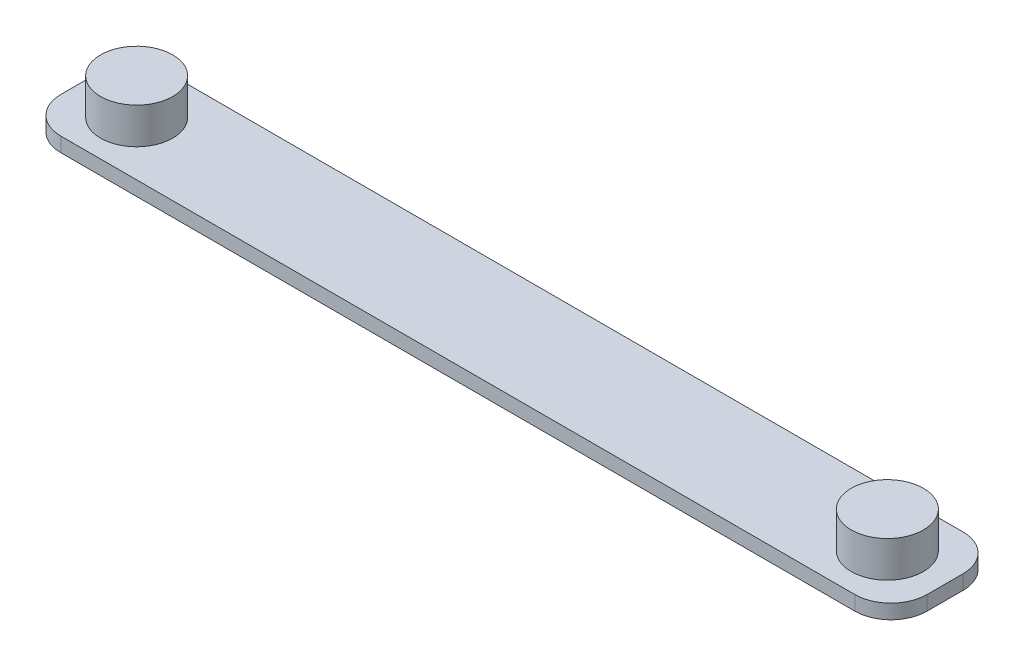
SolidWorks part; units mm, degrees
ref_plane "Front Plane" through (0, 0, 0) normal (0, 0, 1) x (1, 0, 0)
ref_plane "Top Plane" through (0, 0, 0) normal (0, 1, 0) x (1, 0, 0)
ref_plane "Right Plane" through (0, 0, 0) normal (1, 0, 0) x (0, 0, -1)
sketch "Sketch1" plane through (0, 0, 0) normal (0, 1, 0) x (1, 0, 0)
  line L1 (-55, -7.5) -> (55, -7.5)
  line L2 (-60, -2.5) -> (-60, 2.5)
  line L3 (-55, 7.5) -> (55, 7.5)
  line L4 (60, -2.5) -> (60, 2.5)
  arc A0 (-55, -7.5) -> (-60, -2.5) centre (-55, -2.5) cw
  arc A1 (-60, 2.5) -> (-55, 7.5) centre (-55, 2.5) cw
  arc A2 (55, -7.5) -> (60, -2.5) centre (55, -2.5) ccw
  arc A3 (55, 7.5) -> (60, 2.5) centre (55, 2.5) cw
  point P0 (0, 0)
  dimension "D1" = 5
extrude "Boss-Extrude2" add sketch "Sketch1" along normal blind 2 contours L2 A1 L3 A3 L4 A2 L1 A0
sketch "Sketch3" plane through (0, 2, 0) normal (0, 1, 0) x (1, 0, 0)
  line L0 (0, 18.5016) -> (0, -21.8608) construction
  circle A0 centre (52, 0) radius 5
  circle A1 centre (-52, 0) radius 5
extrude "Boss-Extrude3" add sketch "Sketch3" along normal blind 5
